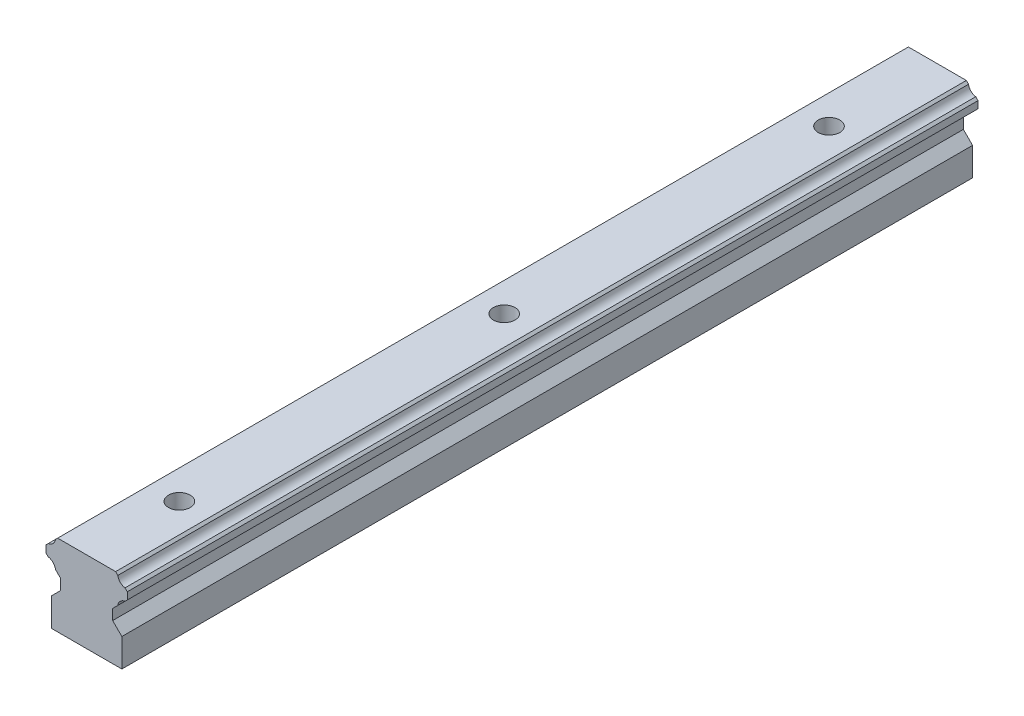
SolidWorks part; units mm, degrees
ref_plane "Front Plane" through (0, 0, 0) normal (0, 0, 1) x (1, 0, 0)
ref_plane "Top Plane" through (0, 0, 0) normal (0, 1, 0) x (1, 0, 0)
ref_plane "Right Plane" through (0, 0, 0) normal (1, 0, 0) x (0, 0, -1)
sketch "Sketch1" plane through (0, 0, 0) normal (0, 0, 1) x (1, 0, 0)
  line B0 (-6.5, 0) -> (6.5, 0)
  line B1 (-6.5, 5.2) -> (-6.5, 0)
  line B2 (6.5, 5.2) -> (6.5, 0)
  line B3 (-9.5, 16) -> (-9.5, 5.2) construction
  line B4 (-6.5, 5.2) -> (-4.8, 6.9)
  line B5 (-4.8, 6.9) -> (-4.8, 8.84)
  line B6 (-4.8, 8.84) -> (-5.7549, 9.7949)
  line B7 (-7.0851, 11.1251) -> (-7.5, 11.54)
  line B8 (-7.5, 11.54) -> (-7.5, 12.85)
  line B9 (-7.5, 12.85) -> (-7.0816, 13.2684)
  line B10 (-5.7554, 14.5946) -> (-5.35, 15)
  line B11 (-5.35, 15) -> (5.35, 15)
  line B12 (5.35, 15) -> (5.7554, 14.5946)
  line B13 (7.0816, 13.2684) -> (7.5, 12.85)
  line B14 (7.5, 12.85) -> (7.5, 11.54)
  line B15 (7.5, 11.54) -> (7.0851, 11.1251)
  line B16 (5.7549, 9.7949) -> (4.8, 8.84)
  line B17 (4.8, 8.84) -> (4.8, 6.9)
  line B18 (4.8, 6.9) -> (6.5, 5.2)
  arc B19 (-5.7549, 9.7949) -> (-7.0851, 11.1251) centre (-7.3, 9.58) ccw
  arc B20 (-7.0816, 13.2684) -> (-5.7554, 14.5946) centre (-7.3, 14.813) ccw
  arc B21 (5.7554, 14.5946) -> (7.0816, 13.2684) centre (7.3, 14.813) ccw
  arc B22 (7.0851, 11.1251) -> (5.7549, 9.7949) centre (7.3, 9.58) ccw
sketch_block_instance "Block-RailTopography-1"
sketch_block "Block-RailTopography" parameters "D1"=15
extrude "Boss-Extrude1" add sketch "Sketch1" along normal blind 156.9999
sketch "Sketch2" plane through (0, 15, 0) normal (0, 1, 0) x (1, 0, 0)
  line L0 (0, 0) -> (0, -41.0979) construction
  line L1 (5.35, 0) -> (-5.35, 0) construction
  circle A0 centre (0, -20) radius 2
  circle A1 centre (0, -79.944) radius 2
  circle A2 centre (0, -139.888) radius 2
  dimension "D2" = 4
  dimension "D1" = 20
  dimension "D3" = 3
extrude "Cut-Extrude1" cut sketch "Sketch2" against normal through all
